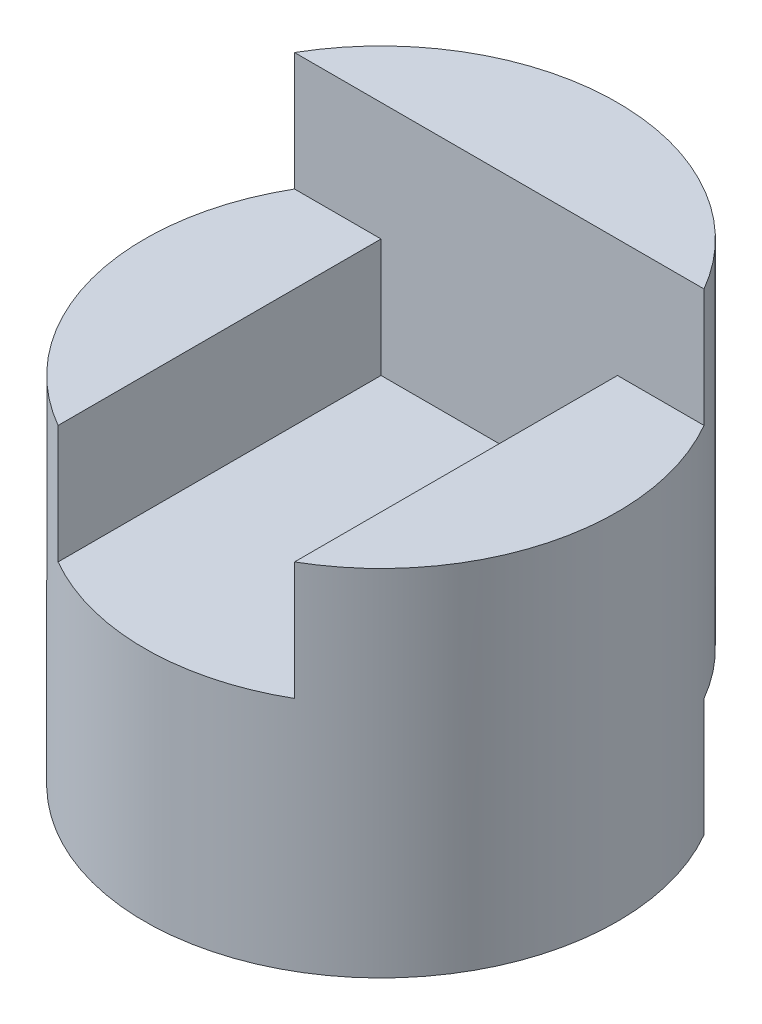
SolidWorks part; units mm, degrees
ref_plane "Front" through (0, 0, 0) normal (0, 0, 1) x (1, 0, 0)
ref_plane "Top" through (0, 0, 0) normal (0, 1, 0) x (1, 0, 0)
ref_plane "Right" through (0, 0, 0) normal (1, 0, 0) x (0, 0, -1)
sketch "Sketch1" plane through (0, 0, 0) normal (0, 1, 0) x (1, 0, 0)
  circle A0 centre (0, 0) radius 2
  dimension "D1" = 4
extrude "Boss-Extrude1" add sketch "Sketch1" along normal blind 4
sketch "Sketch2" plane through (0, 0, 0) normal (0, 0, 1) x (1, 0, 0)
  line L0 (-2, 4) -> (2, 4)
  line L1 (2, 4) -> (2, 3)
  line L2 (2, 0) -> (2, 4) construction
  line L3 (2, 3) -> (1, 3)
  line L4 (1, 3) -> (1, 2)
  line L5 (1, 2) -> (-1, 2)
  line L6 (-1, 2) -> (-1, 3)
  line L7 (-1, 3) -> (-2, 3)
  line L8 (-2, 3) -> (-2, 4)
  dimension "D1" = 1
  dimension "D2" = 1
  dimension "D3" = 1
  dimension "D4" = 1
  dimension "D5" = 1
extrude "Cut-Extrude1" cut sketch "Sketch2" against normal blind 1 and the other way blind 3
sketch "Sketch4" plane through (0, 0, 0) normal (0, -1, 0) x (1, 0, 0)
  line L0 (1.7321, -1) -> (-1.7321, -1)
  arc A0 (1.7321, -1) -> (-1.7321, -1) centre (0, 0) cw
extrude "Cut-Extrude3" cut sketch "Sketch4" against normal blind 1
